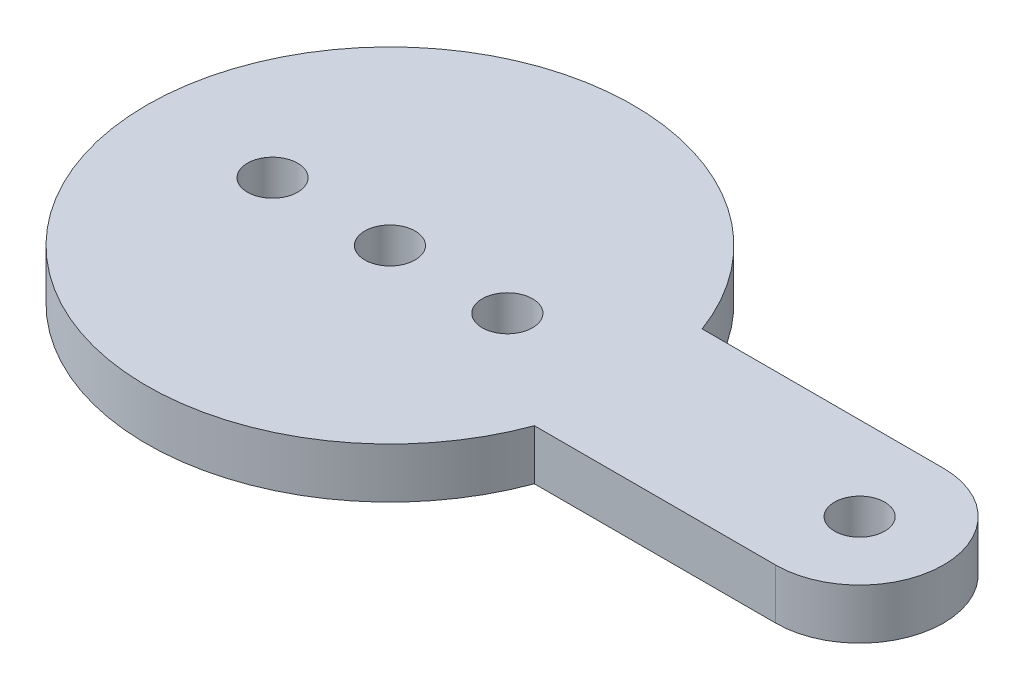
SolidWorks part; units mm, degrees
ref_plane "Front Plane" through (0, 0, 0) normal (0, 0, 1) x (1, 0, 0)
ref_plane "Top Plane" through (0, 0, 0) normal (0, 1, 0) x (1, 0, 0)
ref_plane "Right Plane" through (0, 0, 0) normal (1, 0, 0) x (0, 0, -1)
sketch "Sketch1" plane through (0, 0, 0) normal (0, 1, 0) x (1, 0, 0)
  line L0 (0, 0) -> (28, 0) construction
  line L1 (28, 5) -> (13.6107, 5)
  line L2 (28, -5) -> (13.6107, -5)
  line L3 (0, 0) -> (-7, 0) construction
  arc A0 (13.6107, 5) -> (13.6107, -5) centre (0, 0) ccw
  arc A2 (28, -5) -> (28, 5) centre (28, 0) ccw
  circle A3 centre (28, 0) radius 1.5
  circle A4 centre (0, 0) radius 1.5
  circle A5 centre (7, 0) radius 1.5
  circle A6 centre (-7, 0) radius 1.5
  dimension "D1" = 29
  dimension "D3" = 10
  dimension "D4" = 3
  dimension "D5" = 3
  dimension "D6" = 3
  dimension "D7" = 3
  dimension "D2" = 28
  dimension "D8" = 7
  dimension "D9" = 7
extrude "Boss-Extrude1" add sketch "Sketch1" along normal blind 3
